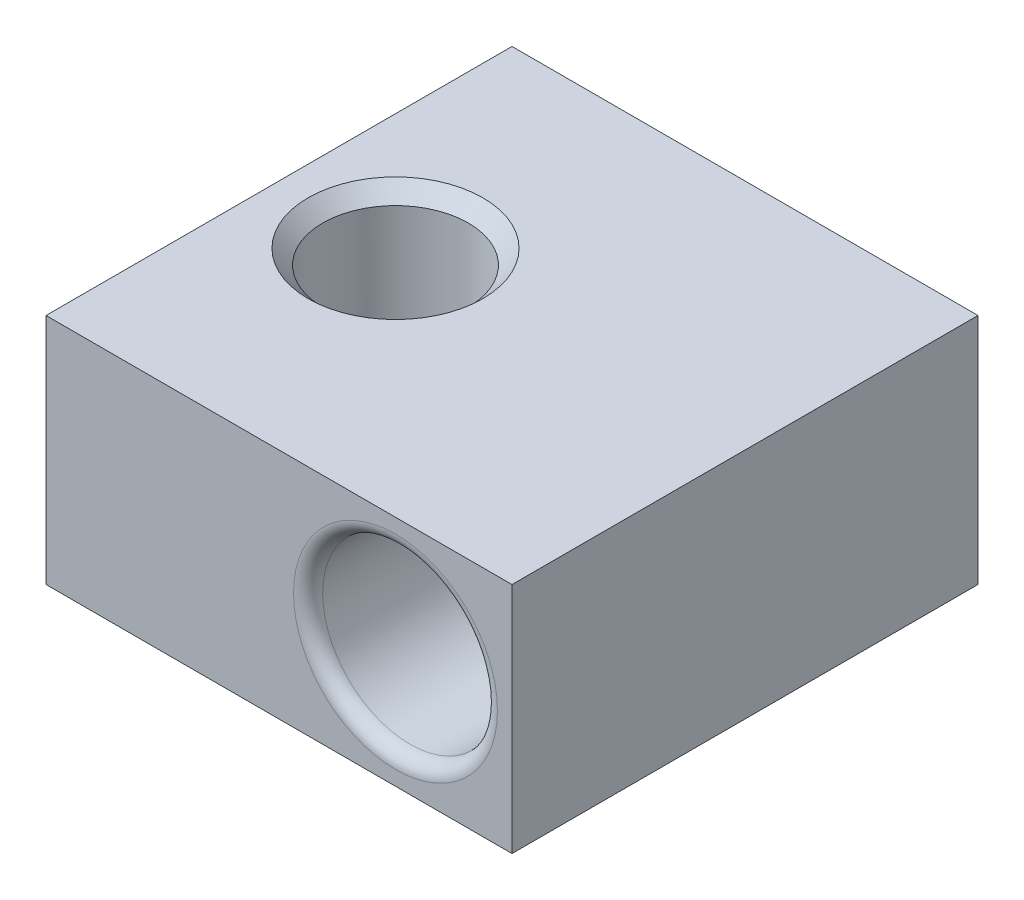
SolidWorks part; units mm, degrees
material "Acier non allié"
ref_plane "Plan de face" through (0, 0, 0) normal (0, 0, 1) x (1, 0, 0)
ref_plane "Plan de dessus" through (0, 0, 0) normal (0, 1, 0) x (1, 0, 0)
ref_plane "Plan de droite" through (0, 0, 0) normal (1, 0, 0) x (0, 0, -1)
sketch "Esquisse1" plane through (0, 0, 0) normal (0, 0, 1) x (1, 0, 0)
  line L1 (0, 0) -> (16, 0)
  line L2 (0, 0) -> (0, 8)
  line L3 (0, 8) -> (16, 8)
  line L4 (16, 0) -> (16, 8)
  circle A0 centre (12, 4) radius 3
  point P8 (16, 4)
  dimension "D3" = 4
  dimension "D4" = 6
  dimension "D1" = 8
  dimension "D2" = 16
extrude "Boss.-Extru.1" add sketch "Esquisse1" along normal blind 16
sketch "Esquisse2" plane through (0, 8, 0) normal (0, 1, 0) x (1, 0, 0)
  line L0 (0, -16) -> (0, 0) construction
  circle A0 centre (4, -8) radius 2.5
  point P4 (0, -8)
  dimension "D1" = 5
  dimension "D2" = 4
extrude "Enlèv. mat.-Extru.1" cut sketch "Esquisse2" against normal through all
chamfer "Chanfrein1" distance 0.5 angle 45 2 edges at (4, 0, 10.5) (4, 8, 10.5)
fillet "Congé1" radius 0.5 2 edges at (15, 4, 0) (15, 4, 16)
